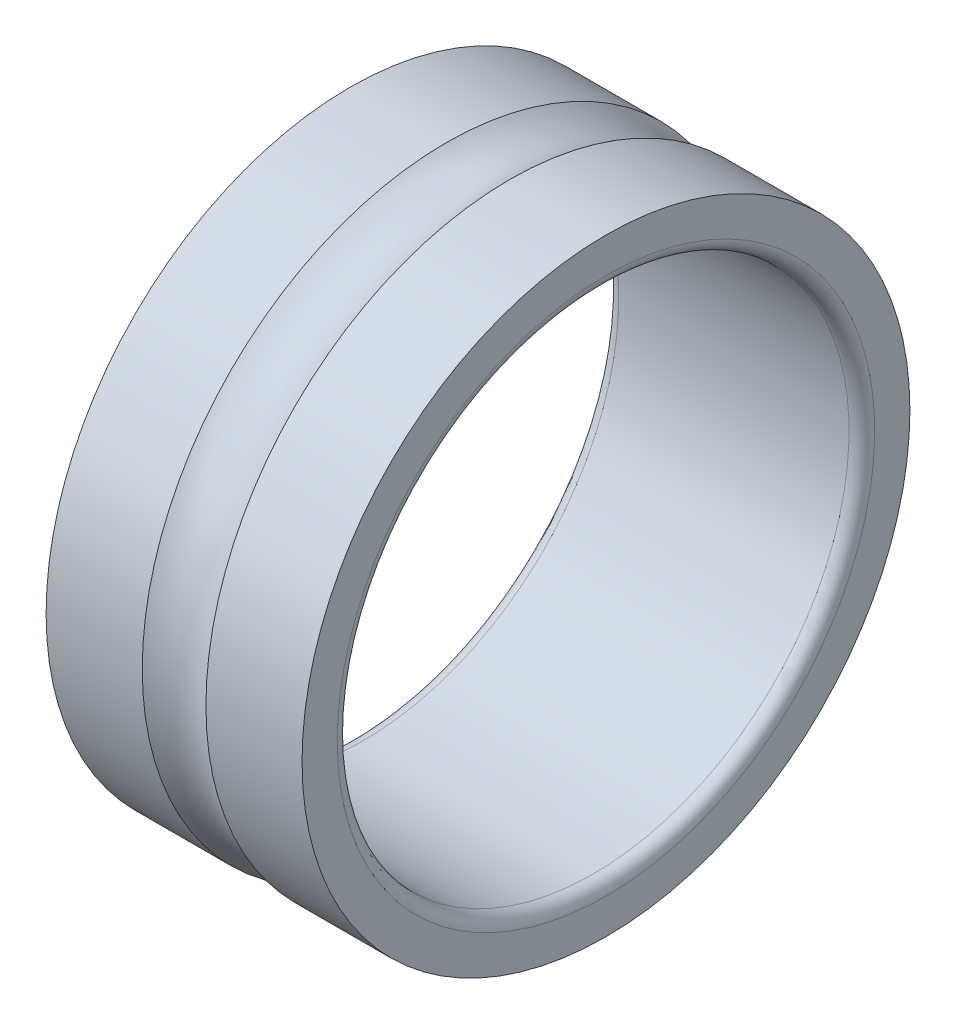
SolidWorks part; units mm, degrees
ref_plane "Front Plane" through (0, 0, 0) normal (0, 0, 1) x (1, 0, 0)
ref_plane "Top Plane" through (0, 0, 0) normal (0, 1, 0) x (1, 0, 0)
ref_plane "Right Plane" through (0, 0, 0) normal (1, 0, 0) x (0, 0, -1)
ref_plane "Plane1" through (0, 0, 0) normal (0, 0, 1) x (1, 0, 0)
sketch "Sketch1" plane through (0, 0, 0) normal (0, 0, 1) x (1, 0, 0)
  line L0 (0, 2.375) -> (0, 2.1)
  line L1 (0.1, 2) -> (1.9, 2)
  line L2 (2, 2.1) -> (2, 2.375)
  line L3 (2, 2.375) -> (1.2487, 2.375)
  line L4 (0.7513, 2.375) -> (0, 2.375)
  line L5 (2, 0) -> (0, 0) construction
  arc A0 (0, 2.1) -> (0.1, 2) centre (0.1, 2.1) ccw
  arc A1 (1.9, 2) -> (2, 2.1) centre (1.9, 2.1) ccw
  arc A2 (1.2487, 2.375) -> (0.7513, 2.375) centre (1, 2.75) cw
revolve "Revolve1" add sketch "Sketch1" angle 360 about L5
